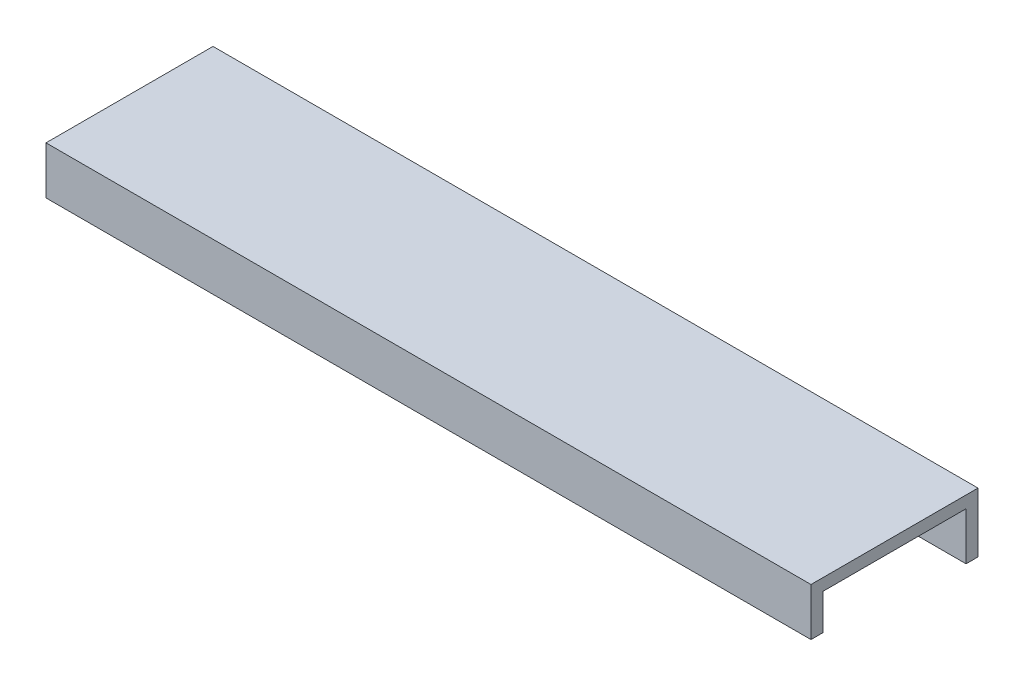
SolidWorks part; units mm, degrees
material "ABS"
ref_plane "Plan de face" through (0, 0, 0) normal (0, 0, 1) x (1, 0, 0)
ref_plane "Plan de dessus" through (0, 0, 0) normal (0, 1, 0) x (1, 0, 0)
ref_plane "Plan de droite" through (0, 0, 0) normal (1, 0, 0) x (0, 0, -1)
sketch "Esquisse1" plane through (0, 0, 0) normal (0, 0, 1) x (1, 0, 0)
  line L0 (-0.004, 129.04) -> (-0.004, 119.04)
  line L1 (-0.004, 129.04) -> (-128.2501, 129.04)
  line L4 (145.0949, 12.3477) -> (-0.004, 119.04) construction
  line L5 (160.0562, 13.7589) -> (3.2768, 129.04) construction
  line L6 (-0.004, 119.04) -> (-128.2501, 119.04)
  line L8 (-0.004, -143.8218) -> (145.0949, 12.3477) construction
  line L9 (7.322, -150.6284) -> (160.0562, 13.7589) construction
  line L10 (3.2768, 129.04) -> (-245.2972, 129.04) construction
  line L12 (-128.2501, 129.04) -> (-128.2501, 119.04)
  line L13 (-0.004, 119.04) -> (-245.2972, 119.04) construction
extrude "Boss.-Extru.2" add sketch "Esquisse1" along normal blind 2
sketch "Esquisse2" plane through (0, 0, 2) normal (0, 0, 1) x (1, 0, 0)
  line L0 (-128.2501, 127.04) -> (2.6206, 127.04)
  line L1 (-128.2501, 129.04) -> (-128.2501, 127.04)
  line L2 (-144.9194, -298.5903) -> (-143.3249, -299.7976)
  line L4 (-0.004, 119.04) -> (-0.004, 129.04)
  line L5 (-0.004, 129.04) -> (-128.2501, 129.04)
  line L7 (-128.2501, 119.04) -> (-0.004, 119.04)
  line L9 (-0.004, 129.04) -> (-128.2501, 129.04)
  line L15 (-0.004, 119.04) -> (-0.004, 129.04)
  line L16 (-128.2501, 129.04) -> (-128.2501, 119.04)
  line L17 (-128.2501, 129.04) -> (-128.2501, 119.04)
  spline S2 degree 3 poles (2.6206, 127.04) (4.1152, 127.0533) (7.1204, 127.0628) (13.0032, 127.0114) (20.2062, 126.8154) (28.5818, 126.3685) (39.403, 125.4888) (52.2776, 123.8538) (66.6908, 121.0221) (80.0699, 117.304) (96.5251, 111.1383) (114.4794, 101.1092) (128.7474, 87.879) (137.771, 75.4462) (143.3145, 65.246) (147.6237, 54.2178) (150.1937, 44.3733) (151.6475, 36.1184) (152.44, 29.7408) (152.8546, 24.2679) (153.0402, 19.8043) (153.0848, 17.528) (153.0949, 16.3951) knots 0.495645 0.495645 0.495645 0.495645 0.49575 0.495854 0.496064 0.496274 0.496483 0.496903 0.497322 0.497742 0.498161 0.499 0.499839 0.500258 0.500677 0.501097 0.501516 0.501726 0.501935 0.502145 0.50225 0.502355 0.502355 0.502355 0.502355
  spline S9 degree 3 poles (153.0949, 16.3951) (153.0949, 15.5541) (153.0946, 14.2819) (153.0954, 12.6283) (153.0923, 10.8328) (153.0475, 8.6133) (152.901, 5.107) (152.5721, 0.8101) (151.7396, -5.8887) (150.1284, -13.9398) (146.3674, -26.1656) (139.5387, -40.2643) (128.3601, -55.5564) (114.6078, -69.6915) (98.5749, -83.2291) (80.4773, -96.7229) (60.5005, -110.6967) (38.8239, -125.6499) (15.6285, -142.0663) (-8.9011, -160.4216) (-34.5774, -181.1879) (-56.7709, -200.8947) (-74.9071, -218.3369) (-88.6753, -232.3161) (-102.585, -247.252) (-114.2734, -260.5449) (-123.6702, -271.7172) (-130.7366, -280.3714) (-136.6417, -287.8232) (-141.3665, -293.922) (-143.7418, -297.0352) (-144.9194, -298.5903) knots -0.012692 -0.012692 -0.012692 -0.012692 -0.00478 -0.000824 0.003131 0.011043 0.018955 0.034778 0.050601 0.082248 0.113895 0.177188 0.240481 0.303774 0.367068 0.430361 0.493654 0.556947 0.620241 0.683534 0.746827 0.81012 0.841767 0.873414 0.90506 0.936707 0.95253 0.968353 0.984177 0.992088 1 1 1 1
  dimension "D1" = 0
extrude "Boss.-Extru.3" add sketch "Esquisse2" along normal blind 24
sketch "Esquisse3" plane through (0, 0, 26) normal (0, 0, 1) x (1, 0, 0)
  line L7 (-128.2501, 121.04) -> (-0.004, 121.04)
  line L12 (-0.004, 119.04) -> (-0.004, 127.04) construction
  line L13 (-0.004, 121.04) -> (-0.004, 129.04)
  line L14 (-0.004, 129.04) -> (-128.2501, 129.04)
  line L15 (-128.2501, 129.04) -> (-128.2501, 121.04)
  line L16 (-128.2501, 127.04) -> (-128.2501, 119.04) construction
extrude "Boss.-Extru.4" add sketch "Esquisse3" along normal blind 2
